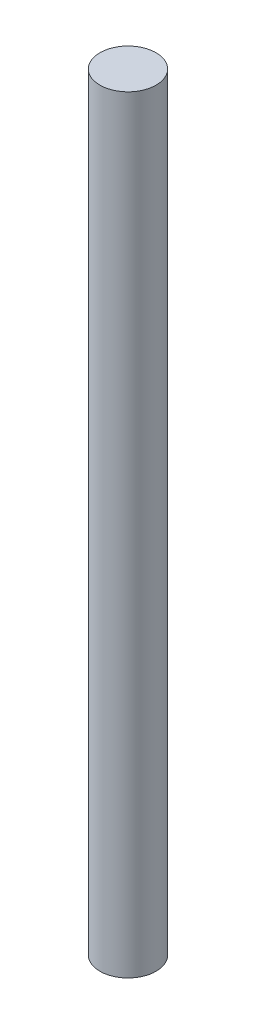
SolidWorks part; units mm, degrees
ref_plane "Front Plane" through (0, 0, 0) normal (0, 0, 1) x (1, 0, 0)
ref_plane "Top Plane" through (0, 0, 0) normal (0, 1, 0) x (1, 0, 0)
ref_plane "Right Plane" through (0, 0, 0) normal (1, 0, 0) x (0, 0, -1)
sketch "Sketch1" plane through (0, 0, 0) normal (0, 1, 0) x (1, 0, 0)
  circle A0 centre (0, 0) radius 3
extrude "Boss-Extrude1" add sketch "Sketch1" along normal blind 82
